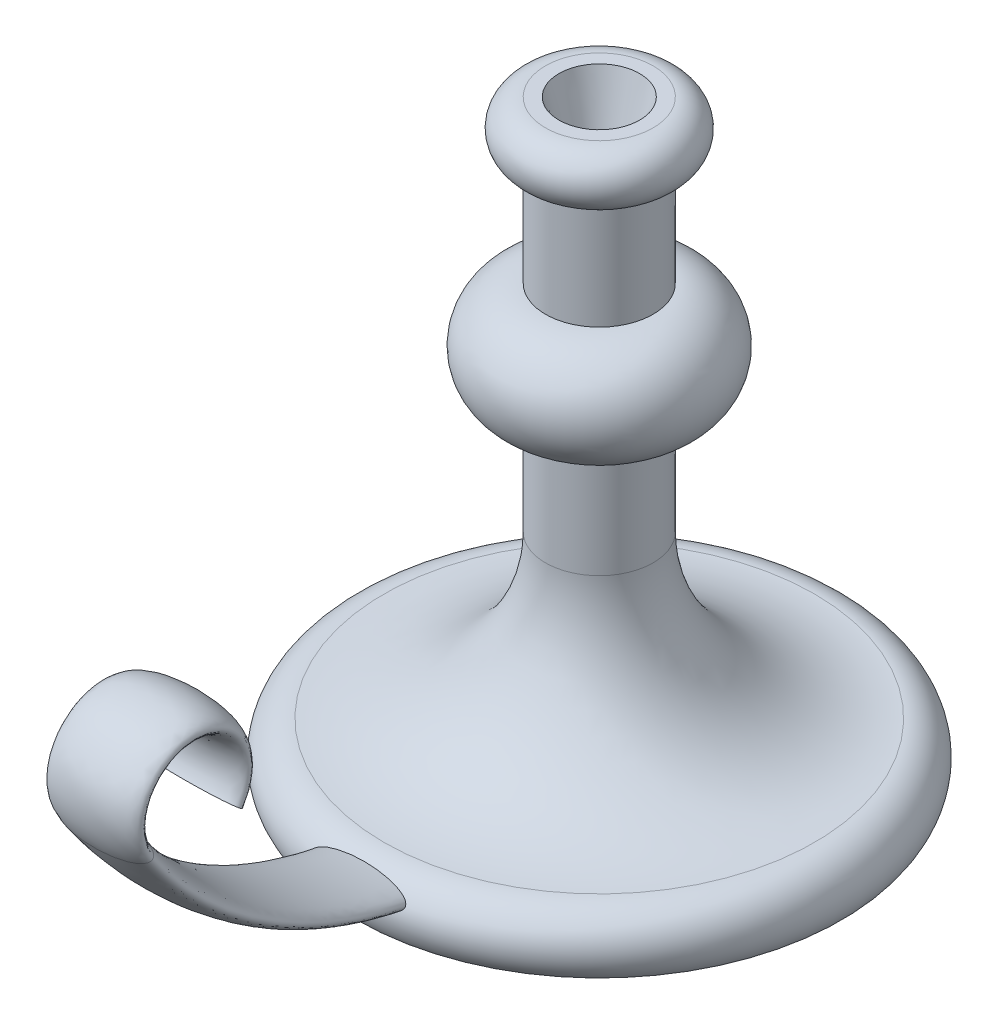
SolidWorks part; units mm, degrees
ref_plane "Front Plane" through (0, 0, 0) normal (0, 0, 1) x (1, 0, 0)
ref_plane "Top Plane" through (0, 0, 0) normal (0, 1, 0) x (1, 0, 0)
ref_plane "Right Plane" through (0, 0, 0) normal (1, 0, 0) x (0, 0, -1)
sketch "Sketch3" plane through (0, 0, 0) normal (0, 0, 1) x (1, 0, 0)
  line L0 (0, 0) -> (0, 220)
  line L1 (0, 220) -> (20, 220)
  line L2 (0, 0) -> (90, 0)
  line L3 (20, 200) -> (20, 160)
  line L4 (20, 120) -> (20, 80)
  arc A0 (20, 220) -> (20, 200) centre (20, 210) cw
  arc A1 (20, 160) -> (20, 120) centre (20, 140) cw
  arc A2 (20, 80) -> (80, 20) centre (80, 80) ccw
  arc A3 (80, 20) -> (90, 0) centre (80, 7.5) cw
  dimension "D4" = 10
  dimension "D5" = 20
  dimension "D7" = 60
  dimension "D8" = 12.5
  dimension "D1" = 220
  dimension "D2" = 20
  dimension "D3" = 90
  dimension "D6" = 40
  dimension "D9" = 80
revolve "Revolve1" add sketch "Sketch3" angle 360 about L0
sketch "Sketch8" plane through (0, 0, 0) normal (1, 0, 0) x (0, 0, -1)
  line L0 (0, 10) -> (-60, 10)
  line L1 (0, 227.4356) -> (0, 175.1288) construction
  line L2 (0, 200) -> (0, 160) construction
  line L3 (-90, 0) -> (90, 0) construction
  arc A0 (-60, 10) -> (-183.5921, 75) centre (-60, 160) cw
  arc A1 (-183.5921, 75) -> (-150.6342, 75) centre (-167.1131, 86.3333) cw
  dimension "D2" = 150
  dimension "D4" = 10
  dimension "D1" = 60
  dimension "D3" = 65
sketch "Sketch9" plane through (0, 0, 0) normal (0, 0, 1) x (1, 0, 0)
  ellipse E0 centre (0, 10) end of major axis (17.5, 10) minor radius 5
  dimension "D1" = 10
  dimension "D2" = 35
sweep "Sweep2" add profiles "Sketch9" path "Sketch8"
sketch "Sketch18" plane through (0, 220, 0) normal (0, 1, 0) x (1, 0, 0)
  circle A0 centre (0, 0) radius 15
  dimension "D1" = 30
extrude "Cut-Extrude1" cut sketch "Sketch18" against normal blind 25 draft 15
